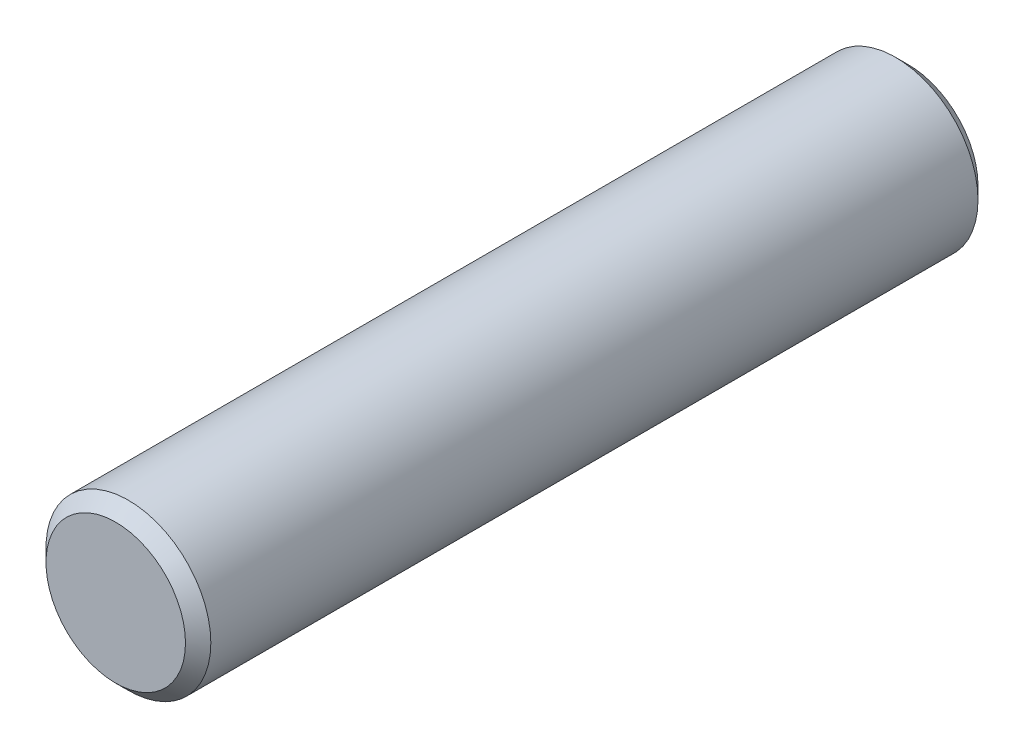
SolidWorks part; units mm, degrees
ref_plane "Front" through (0, 0, 0) normal (0, 0, 1) x (1, 0, 0)
ref_plane "Top" through (0, 0, 0) normal (0, 1, 0) x (1, 0, 0)
ref_plane "Right" through (0, 0, 0) normal (1, 0, 0) x (0, 0, -1)
sketch "Sketch1" plane through (0, 0, 0) normal (0, 0, 1) x (1, 0, 0)
  circle A0 centre (0, 0) radius 1.651
  dimension "D1" = 3.302
extrude "Boss-Extrude1" add sketch "Sketch1" against normal blind 15.875
chamfer "Chamfer1" distance 0.254 angle 45 2 edges at (1.651, 0, 0) (1.651, 0, -15.875)
